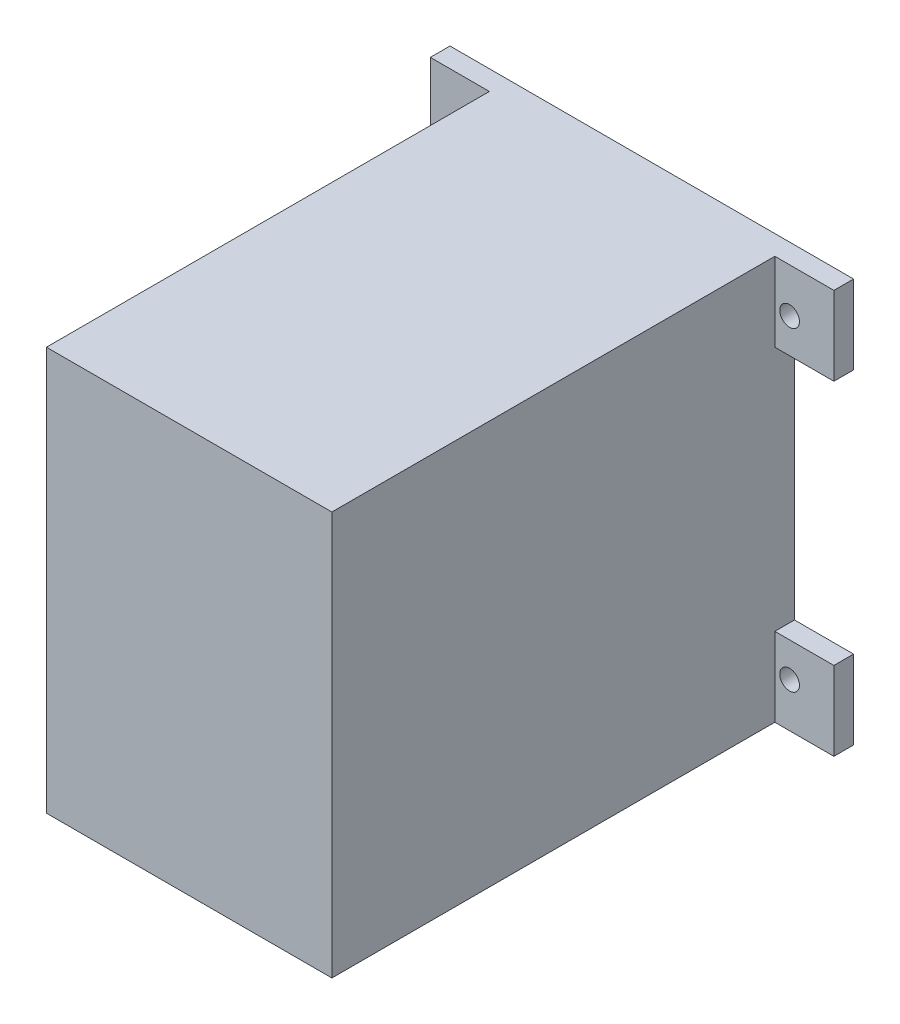
SolidWorks part; units mm, degrees
ref_plane "正面" through (0, 0, 0) normal (0, 0, 1) x (1, 0, 0)
ref_plane "平面" through (0, 0, 0) normal (0, 1, 0) x (1, 0, 0)
ref_plane "右側面" through (0, 0, 0) normal (1, 0, 0) x (0, 0, -1)
sketch "ｽｹｯﾁ1" plane through (0, 0, 0) normal (0, 0, 1) x (1, 0, 0)
  line L1 (14.5, -20.5) -> (-14.5, -20.5)
  line L2 (14.5, -20.5) -> (14.5, 20.5)
  line L3 (14.5, 20.5) -> (-14.5, 20.5)
  line L4 (-14.5, -20.5) -> (-14.5, 20.5)
  line L5 (14.5, -20.5) -> (-14.5, 20.5) construction
  line L6 (14.5, 20.5) -> (-14.5, -20.5) construction
  point P0 (0, 0)
  dimension "D1" = 41
  dimension "D2" = 29
extrude "ﾎﾞｽ - 押し出し1" add sketch "ｽｹｯﾁ1" along normal blind 47
sketch "ｽｹｯﾁ2" plane through (0, 0, 0) normal (0, 0, 1) x (1, 0, 0)
  line L1 (13.25, -19.25) -> (-13.25, -19.25)
  line L2 (13.25, -19.25) -> (13.25, 19.25)
  line L3 (13.25, 19.25) -> (-13.25, 19.25)
  line L4 (-13.25, -19.25) -> (-13.25, 19.25)
  line L5 (13.25, -19.25) -> (-13.25, 19.25) construction
  line L6 (13.25, 19.25) -> (-13.25, -19.25) construction
  point P0 (0, 0)
  dimension "D1" = 26.5
  dimension "D2" = 38.5
extrude "ｶｯﾄ - 押し出し1" cut sketch "ｽｹｯﾁ2" along normal blind 46
sketch "ｽｹｯﾁ3" plane through (0, 0, 0) normal (0, 0, 1) x (1, 0, 0)
  line L0 (14.5, 20.5) -> (-14.5, 20.5) construction
  line L1 (-0.8522, 3.5) -> (1.1478, 3.5)
  line L2 (-0.8522, 3.5) -> (-0.8522, 10.5)
  line L3 (-0.8522, 10.5) -> (1.1478, 10.5)
  line L4 (1.1478, 3.5) -> (1.1478, 10.5)
  line L5 (-0.8522, 3.5) -> (1.1478, 10.5) construction
  line L6 (-0.8522, 10.5) -> (1.1478, 3.5) construction
  point P0 (0.1478, 7)
  dimension "D1" = 7
  dimension "D2" = 2
  dimension "D3" = 10
sketch "ｽｹｯﾁ4" plane through (0, 0, 0) normal (0, 0, 1) x (1, 0, 0)
  line L0 (14.5, -20.5) -> (14.5, 20.5) construction
  line L1 (14.5, 20.5) -> (20.5, 20.5)
  line L2 (14.5, 20.5) -> (14.5, 12.5)
  line L3 (14.5, 12.5) -> (20.5, 12.5)
  line L4 (20.5, 20.5) -> (20.5, 12.5)
  line L5 (14.5, -20.5) -> (20.5, -20.5)
  line L6 (14.5, -20.5) -> (14.5, -12.5)
  line L7 (14.5, -12.5) -> (20.5, -12.5)
  line L8 (20.5, -20.5) -> (20.5, -12.5)
  line L9 (-14.5, -20.5) -> (14.5, -20.5) construction
  line L10 (-14.5, -20.5) -> (-20.5, -20.5)
  line L11 (-14.5, -20.5) -> (-14.5, -12.5)
  line L12 (-14.5, -12.5) -> (-20.5, -12.5)
  line L13 (-20.5, -20.5) -> (-20.5, -12.5)
  line L14 (-14.5, 20.5) -> (-20.5, 20.5)
  line L15 (-14.5, 20.5) -> (-14.5, 12.5)
  line L16 (-14.5, 12.5) -> (-20.5, 12.5)
  line L17 (-20.5, 20.5) -> (-20.5, 12.5)
  dimension "D1" = 6
  dimension "D2" = 8
  dimension "D3" = 8
  dimension "D4" = 6
  dimension "D5" = 6
  dimension "D6" = 8
  dimension "D7" = 8
  dimension "D8" = 6
  dimension "D9" = 0
extrude "ﾎﾞｽ - 押し出し2" add sketch "ｽｹｯﾁ4" along normal blind 2
sketch "ｽｹｯﾁ5" plane through (0, 0, 0) normal (0, 0, 1) x (1, 0, 0)
  line L0 (-14.5, 20.5) -> (-20.5, 20.5) construction
  line L1 (-20.5, 20.5) -> (-20.5, 12.5) construction
  line L2 (-14.5, -12.5) -> (-20.5, -12.5) construction
  line L3 (20.5, -20.5) -> (20.5, -12.5) construction
  line L4 (-20.5, -12.5) -> (-20.5, -20.5) construction
  line L5 (20.5, -12.5) -> (14.5, -12.5) construction
  line L6 (20.5, 12.5) -> (20.5, 20.5) construction
  line L7 (20.5, 20.5) -> (14.5, 20.5) construction
  circle A0 centre (-16, 16) radius 1
  circle A1 centre (-16, -16) radius 1
  circle A2 centre (16, -16) radius 1
  circle A3 centre (16, 16) radius 1
  dimension "D1" = 4.5
  dimension "D2" = 4.5
  dimension "D3" = 3.5
  dimension "D4" = 2
  dimension "D5" = 2
  dimension "D6" = 4.5
  dimension "D7" = 2
  dimension "D8" = 2
  dimension "D9" = 4.5
  dimension "D10" = 3.5
  dimension "D11" = 4.5
  dimension "D12" = 4.5
extrude "ｶｯﾄ - 押し出し4" cut sketch "ｽｹｯﾁ5" along normal blind 2
